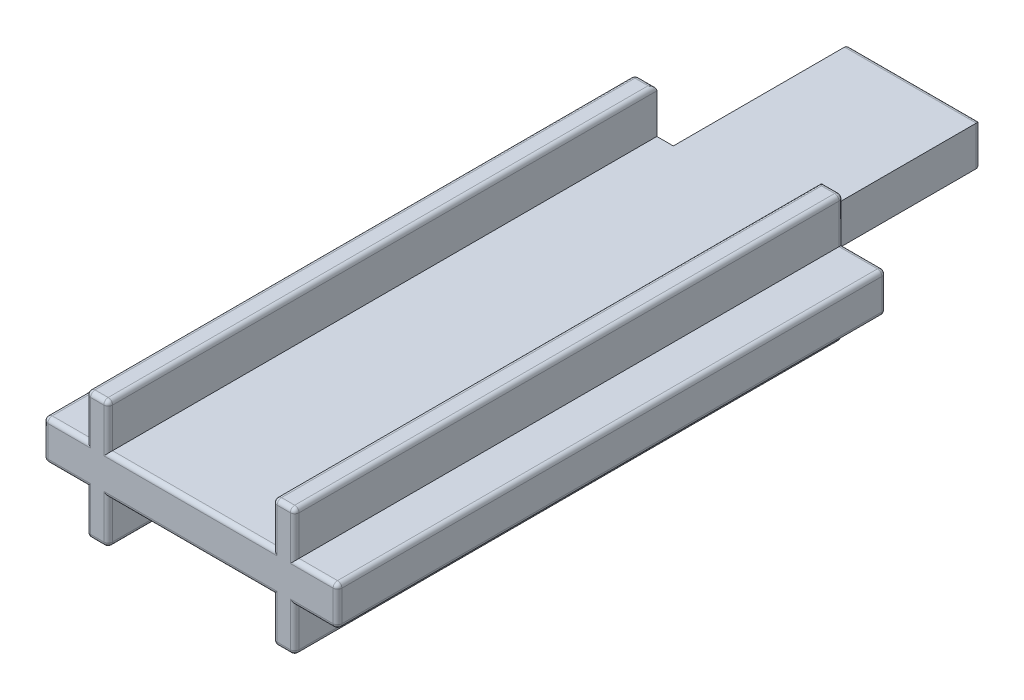
SolidWorks part; units mm, degrees
ref_plane "Ebene vorne" through (0, 0, 0) normal (0, 0, 1) x (1, 0, 0)
ref_plane "Ebene oben" through (0, 0, 0) normal (0, 1, 0) x (1, 0, 0)
ref_plane "Ebene rechts" through (0, 0, 0) normal (1, 0, 0) x (0, 0, -1)
sketch "Skizze1" plane through (0, 0, 0) normal (0, 0, 1) x (1, 0, 0)
  line L0 (-4.75, 0.9) -> (-6.7, 0.9)
  line L1 (6.7, -0.9) -> (4.75, -0.9)
  line L2 (6.7, -0.9) -> (6.7, 0.9)
  line L3 (6.7, 0.9) -> (4.75, 0.9)
  line L4 (-6.7, -0.9) -> (-6.7, 0.9)
  line L5 (6.7, -0.9) -> (-6.7, 0.9) construction
  line L6 (6.7, 0.9) -> (-6.7, -0.9) construction
  line L7 (-4.75, -2.9) -> (-3.75, -2.9)
  line L8 (-4.75, -2.9) -> (-4.75, -0.9)
  line L9 (-4.75, 2.9) -> (-3.75, 2.9)
  line L10 (-3.75, -2.9) -> (-3.75, -0.9)
  line L11 (-4.75, -2.9) -> (-3.75, 2.9) construction
  line L12 (-4.75, 2.9) -> (-3.75, -2.9) construction
  line L13 (4.75, -2.9) -> (3.75, -2.9)
  line L14 (4.75, -2.9) -> (4.75, -0.9)
  line L15 (4.75, 2.9) -> (3.75, 2.9)
  line L16 (3.75, -2.9) -> (3.75, -0.9)
  line L17 (4.75, -2.9) -> (3.75, 2.9) construction
  line L18 (4.75, 2.9) -> (3.75, -2.9) construction
  line L19 (-4.75, -0.9) -> (-6.7, -0.9)
  line L20 (-4.75, 0.9) -> (-4.75, 2.9)
  line L21 (-3.75, 0.9) -> (-3.75, 2.9)
  line L22 (3.75, -0.9) -> (-3.75, -0.9)
  line L23 (3.75, 0.9) -> (3.75, 2.9)
  line L24 (4.75, 0.9) -> (4.75, 2.9)
  line L25 (3.75, 0.9) -> (-3.75, 0.9)
  point P0 (0, 0)
  point P5 (-4.25, 0)
  point P11 (4.25, 0)
  dimension "D1" = 1.8
  dimension "D2" = 5.8
  dimension "D3" = 13.4
  dimension "D4" = 9.5
  dimension "D5" = 1
  dimension "D6" = 4.75
extrude "Aufsatz-Linear austragen1" add sketch "Skizze1" along normal blind 25
sketch "Skizze2" plane through (0, 0, 0) normal (0, 0, -1) x (-1, 0, 0)
  line L0 (-3.75, 0.9) -> (3.75, 0.9) construction
  line L1 (3, -0.9) -> (-3, -0.9)
  line L2 (3, -0.9) -> (3, 0.9)
  line L3 (3, 0.9) -> (-3, 0.9)
  line L4 (-3, -0.9) -> (-3, 0.9)
  line L5 (3, -0.9) -> (-3, 0.9) construction
  line L6 (3, 0.9) -> (-3, -0.9) construction
  point P0 (0, 0)
  dimension "D1" = 6
extrude "Aufsatz-Linear austragen2" add sketch "Skizze2" along normal blind 8
sketch "Skizze3" plane through (0, 0, 25) normal (0, 0, 1) x (1, 0, 0)
  line L1 (-3.75, -0.9) -> (3.75, -0.9)
  line L2 (-3.75, -0.9) -> (-3.75, -0.75)
  line L3 (-3.75, -0.75) -> (3.75, -0.75)
  line L4 (3.75, -0.9) -> (3.75, -0.75)
  line L5 (3.75, 0.9) -> (-3.75, 0.9)
  line L6 (3.75, 0.9) -> (3.75, 0.75)
  line L7 (3.75, 0.75) -> (-3.75, 0.75)
  line L8 (-3.75, 0.9) -> (-3.75, 0.75)
  dimension "D1" = 1.5
  dimension "D2" = 0.75
fillet "Verrundung1" radius 0.2 50 edges at (-5.725, 0.9, 25) (-4.75, 1.9, 25) (-3.75, 1.9, 25) (0, 0.9, 25) (3.75, 1.9, 25) (4.75, 1.9, 25) (5.725, 0.9, 25) (5.725, -0.9, 25) (4.75, -1.9, 25) (3.75, -1.9, 25) (0, -0.9, 25) (-3.75, -1.9, 25) (-4.75, -1.9, 25) (-5.725, -0.9, 25) (0, 0.9, -8) (-3, 0, -8) (0, -0.9, -8) (3, 0, -8) (-6.7, 0.9, 12.5) (-6.7, 0, 25) (-6.7, -0.9, 12.5) (-6.7, 0, 0) (6.7, -0.9, 12.5) (6.7, 0, 25) (6.7, 0.9, 12.5) (6.7, 0, 0) (-4.75, -2.9, 12.5) (-3.75, -2.9, 12.5) (-4.25, -2.9, 0) (3.75, -2.9, 12.5) (4.75, -2.9, 12.5) (4.25, -2.9, 0) (-3.75, 2.9, 12.5) (-4.75, 2.9, 12.5) (-4.25, 2.9, 0) (4.75, 2.9, 12.5) (3.75, 2.9, 12.5) (4.25, 2.9, 0) (4.75, 1.9, 0) (5.725, 0.9, 0) (5.725, -0.9, 0) (4.75, -1.9, 0) (-4.75, 1.9, 0) (-4.75, -1.9, 0) (-5.725, 0.9, 0) (-5.725, -0.9, 0) (-4.25, -2.9, 25) (4.25, -2.9, 25) (-4.25, 2.9, 25) (4.25, 2.9, 25)
